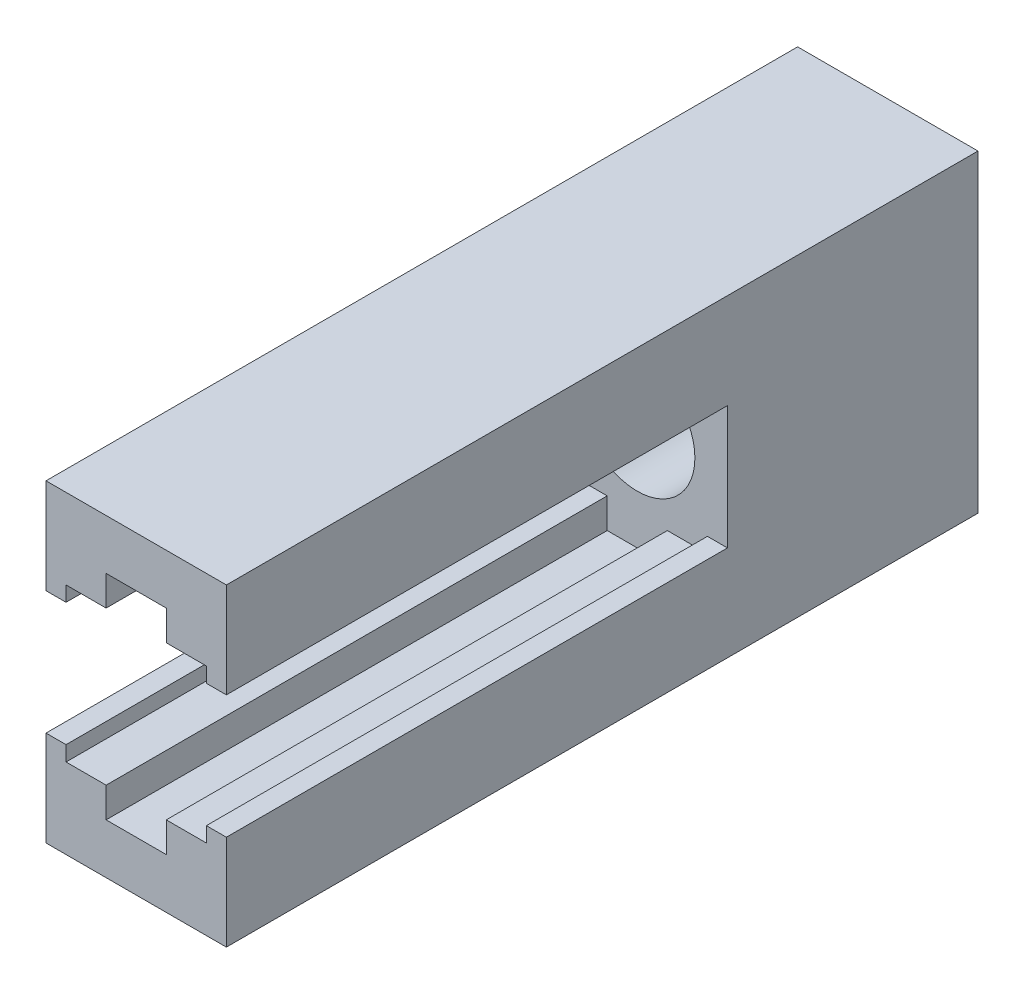
SolidWorks part; units mm, degrees
ref_plane "Top Plane" through (0, 0, 0) normal (0, 0, 1) x (1, 0, 0)
ref_plane "Right Plane" through (0, 0, 0) normal (0, 1, 0) x (1, 0, 0)
ref_plane "Front Plane" through (0, 0, 0) normal (1, 0, 0) x (0, 0, -1)
sketch "Sketch2" plane through (0, 0, 0) normal (0, 0, 1) x (1, 0, 0)
  line L0 (0, -10.65) -> (0, 0) construction
  line L1 (-3, -10.65) -> (3, -10.65)
  line L3 (-9, -15.65) -> (9, -15.65)
  line L6 (-9, -15.65) -> (-9, -7.65)
  line L7 (-7, -7.65) -> (-3, -7.65)
  line L8 (-3, -10.65) -> (-3, -7.65)
  line L10 (9, -15.65) -> (9, -7.65)
  line L11 (7, -7.65) -> (3, -7.65)
  line L12 (3, -10.65) -> (3, -7.65)
  line L13 (-9, -7.65) -> (-9, -6.15)
  line L14 (-9, -6.15) -> (-7, -6.15)
  line L15 (-7, -6.15) -> (-7, -7.65)
  line L16 (9, -7.65) -> (9, -6.15)
  line L17 (9, -6.15) -> (7, -6.15)
  line L18 (7, -6.15) -> (7, -7.65)
  line L19 (-9, -7.65) -> (-7, -7.65) construction
  dimension "D1" = 3
  dimension "D2" = 6
  dimension "D3" = 8
  dimension "D4" = 18
  dimension "D5" = 7.65
  dimension "D6" = 14
  dimension "D7" = 1.5
extrude "Boss-Extrude1" add sketch "Sketch2" along normal blind 50
mirror "Mirror2" about plane through (0, 0, 0) normal (0, 1, 0) of bodies 102
sketch "Sketch3" plane through (0, 0, 0) normal (0, 0, -1) x (-1, 0, 0)
  line L1 (-9, -15.65) -> (9, -15.65)
  line L2 (-9, -15.65) -> (-9, 15.65)
  line L3 (-9, 15.65) -> (9, 15.65)
  line L4 (9, -15.65) -> (9, 15.65)
extrude "Boss-Extrude2" add sketch "Sketch3" along normal blind 25
sketch "Sketch4" plane through (0, 0, 0) normal (0, 0, 1) x (1, 0, 0)
  circle A0 centre (0, 0) radius 5.75
  dimension "D1" = 11.5
extrude "Cut-Extrude1" cut sketch "Sketch4" against normal blind 16
sketch "Sketch5" plane through (0, 0, -16) normal (0, 0, 1) x (1, 0, 0)
  circle A0 centre (0, 0) radius 3.5
  dimension "D1" = 7
extrude "Cut-Extrude2" cut sketch "Sketch5" against normal through all
